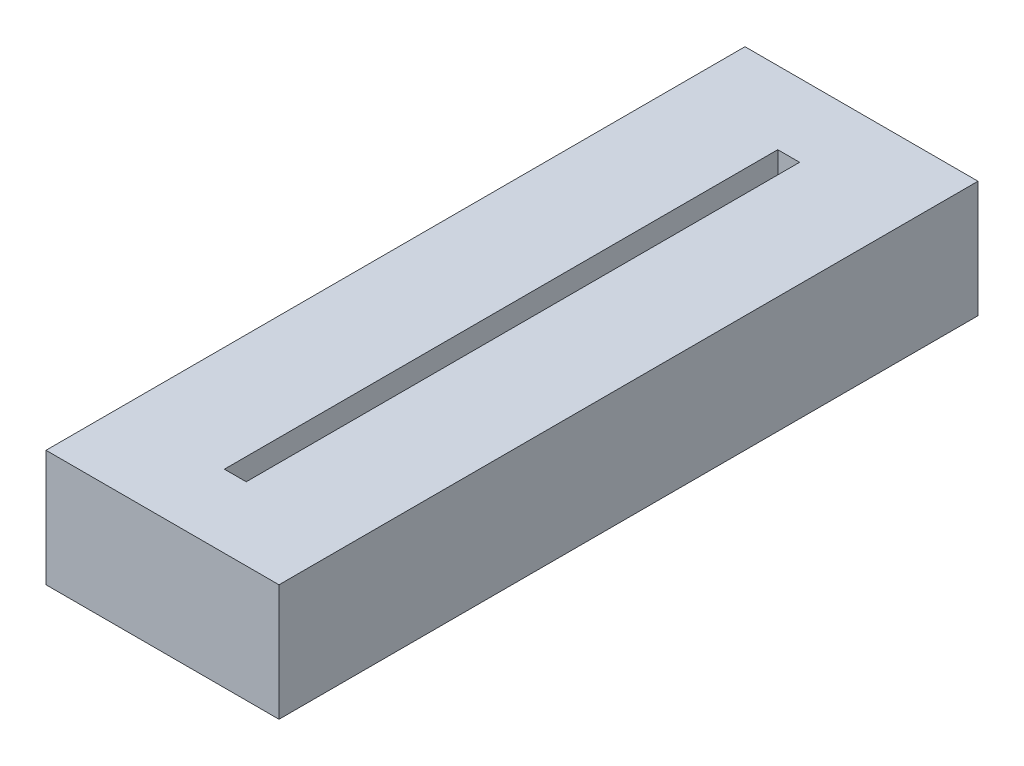
SolidWorks part; units mm, degrees
material "Pine"
ref_plane "Front Plane" through (0, 0, 0) normal (0, 0, 1) x (1, 0, 0)
ref_plane "Top Plane" through (0, 0, 0) normal (0, 1, 0) x (1, 0, 0)
ref_plane "Right Plane" through (0, 0, 0) normal (1, 0, 0) x (0, 0, -1)
sketch "Sketch1" plane through (0, 0, 0) normal (0, 0, 1) x (1, 0, 0)
  line L0 (0, 0) -> (101.6, 0)
  line L1 (101.6, 0) -> (101.6, 50.8)
  line L2 (101.6, 50.8) -> (0, 50.8)
  line L3 (0, 50.8) -> (0, 0)
  dimension "D1" = 50.8
  dimension "D2" = 101.6
extrude "Boss-Extrude1" add sketch "Sketch1" along normal blind 304.8
sketch "Sketch2" plane through (0, 50.8, 0) normal (0, 1, 0) x (1, 0, 0)
  line L0 (46.0375, -41.275) -> (46.0375, -31.75)
  line L1 (46.0375, -263.525) -> (46.0375, -273.05)
  line L2 (46.0375, -31.75) -> (55.5625, -31.75)
  line L3 (46.0375, -273.05) -> (55.5625, -273.05)
  line L5 (55.5625, -41.275) -> (55.5625, -263.525)
  line L8 (46.0375, -41.275) -> (46.0375, -263.525)
  line L10 (55.5625, -31.75) -> (55.5625, -41.275)
  line L11 (55.5625, -273.05) -> (55.5625, -263.525)
  dimension "D1" = 9.525
  dimension "D2" = 9.525
extrude "Cut-Extrude1" cut sketch "Sketch2" against normal blind 19.05
